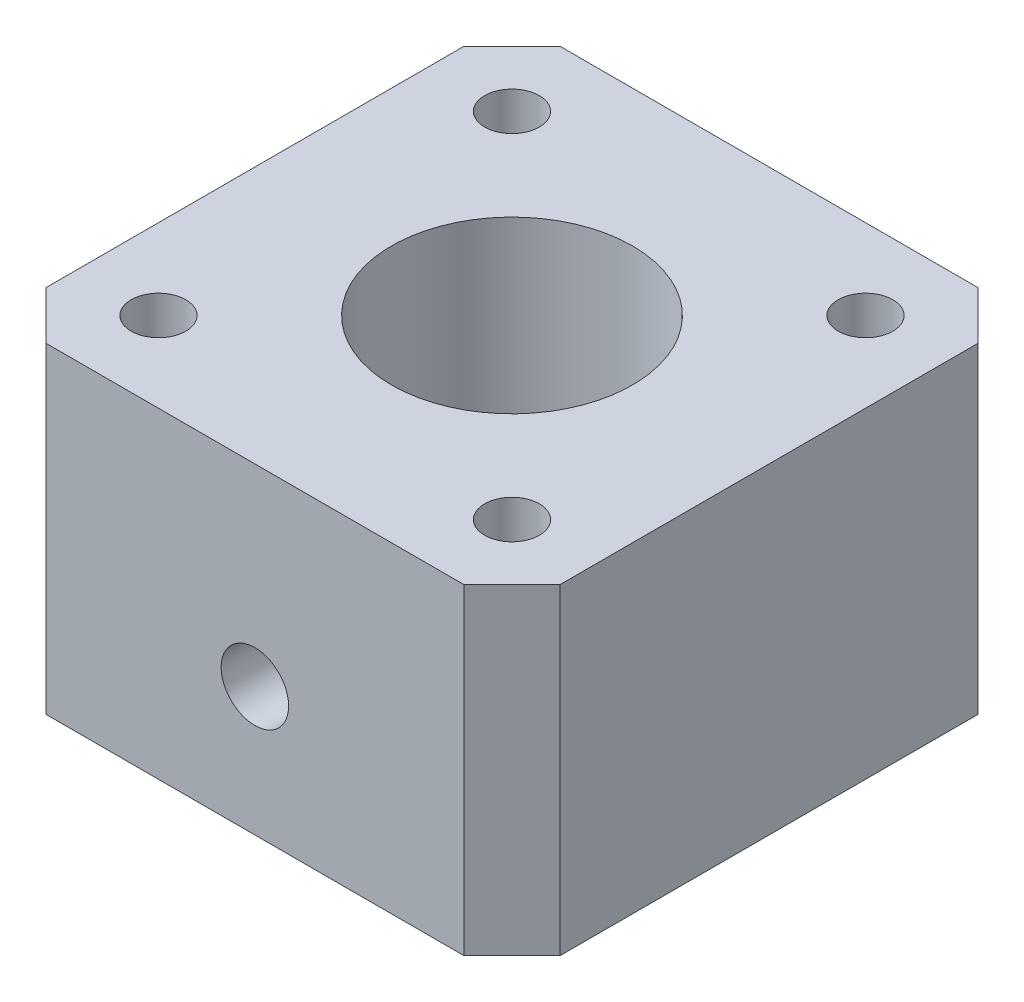
SolidWorks part; units mm, degrees
ref_plane "Front Plane" through (0, 0, 0) normal (0, 0, 1) x (1, 0, 0)
ref_plane "Top Plane" through (0, 0, 0) normal (0, 1, 0) x (1, 0, 0)
ref_plane "Right Plane" through (0, 0, 0) normal (1, 0, 0) x (0, 0, -1)
sketch "Sketch1" plane through (0, 0, 0) normal (0, 1, 0) x (1, 0, 0)
  line L1 (-16, -16) -> (16, -16)
  line L2 (-16, -16) -> (-16, 16)
  line L3 (-16, 16) -> (16, 16)
  line L4 (16, -16) -> (16, 16)
  line L5 (-16, -16) -> (16, 16) construction
  line L6 (-16, 16) -> (16, -16) construction
  line L7 (-11, 11) -> (11, 11) construction
  line L8 (-11, 11) -> (-11, -11) construction
  line L9 (-11, -11) -> (11, -11) construction
  line L10 (11, 11) -> (11, -11) construction
  line L11 (-11, 11) -> (11, -11) construction
  line L12 (-11, -11) -> (11, 11) construction
  circle A0 centre (0, 0) radius 7.5
  circle A1 centre (11, -11) radius 3 construction
  circle A2 centre (11, -11) radius 5 construction
  point P0 (0, 0)
  dimension "D1" = 15
  dimension "D3" = 6
  dimension "D4" = 2
  dimension "D2" = 22
extrude "Boss-Extrude1" add sketch "Sketch1" along normal blind 20
sketch "Sketch2" plane through (0, 0, 0) normal (0, -1, 0) x (-1, 0, 0)
  point P0 (-11, -11)
  point P3 (11, -11)
  point P6 (11, 11)
  point P9 (-11, 11)
hole_wizard "CBORE for M3 SHCS1" positions "Sketch2" profile "Sketch3" counterbore size "M3" standard "ANSI Metric" end condition through all
sketch "Sketch3" plane through (11, 0, 11) normal (1, 0, 0) x (0, 0, -1)
  line L0 (0, 0) -> (0, 20)
  line L1 (0, 20) -> (1.7, 20)
  line L3 (1.7, 20) -> (1.7, 3)
  line L4 (1.7, 3) -> (3.25, 3)
  line L5 (3.25, 3) -> (3.25, 0)
  line L7 (3.25, 0) -> (0, 0)
  line L11 (0, -6.35) -> (0, 107.95) construction
  dimension "Thru Hole Dia." = 3.4
  dimension "Thru Hole Depth" = 20
  dimension "C'Bore Dia." = 6.5
  dimension "C'Bore Depth" = 3
sketch "Sketch5" plane through (0, 0, 16) normal (0, 0, 1) x (1, 0, 0)
  line L0 (0, 8) -> (0, 0) construction
  line L1 (-16, 0) -> (16, 0) construction
  point P0 (0, 8)
  dimension "D1" = 8
hole_wizard "M5x0.8 Tapped Hole1" positions "Sketch5" profile "Sketch6" tap size "M5x0.8" standard "ANSI Metric"
sketch "Sketch6" plane through (0, 8, 16) normal (1, 0, 0) x (0, -1, 0)
  line L0 (0, 0) -> (0, 8.5)
  line L1 (0, 8.5) -> (2.1, 8.5)
  line L2 (2.1, 8.5) -> (2.1, 0)
  line L5 (2.1, 0) -> (0, 0)
  line L11 (0, -6.35) -> (0, 107.95) construction
  dimension "Thru Tap Drill Dia." = 4.2
  dimension "Thru Tap Drill Depth" = 8.5
cosmetic thread "Hole Thread1"
chamfer "Chamfer1" distance 3 angle 45 4 edges at (-16, 10, -16) (-16, 10, 16) (16, 10, -16) (16, 10, 16)
